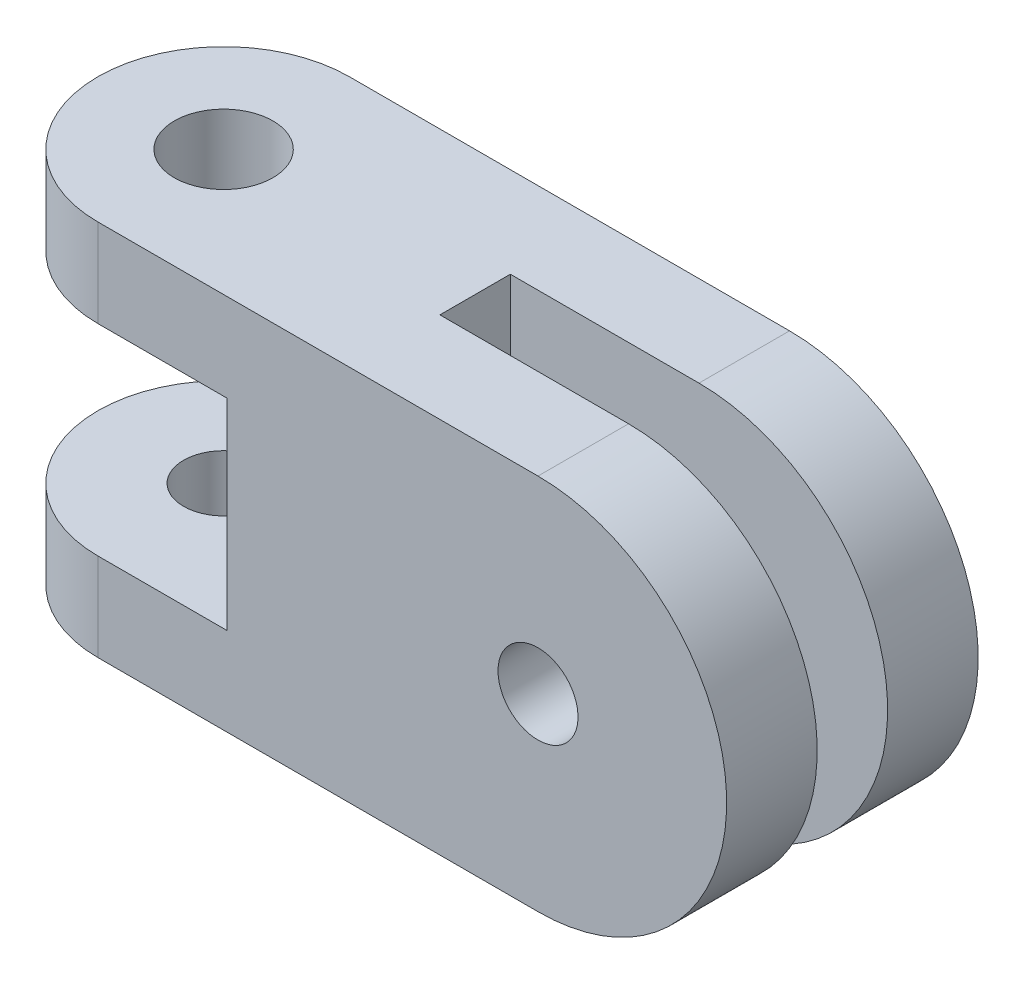
SolidWorks part; units mm, degrees
ref_plane "Front Plane" through (0, 0, 0) normal (0, 0, 1) x (1, 0, 0)
ref_plane "Top Plane" through (0, 0, 0) normal (0, 1, 0) x (1, 0, 0)
ref_plane "Right Plane" through (0, 0, 0) normal (1, 0, 0) x (0, 0, -1)
sketch "Sketch1" plane through (0, 0, 0) normal (0, 1, 0) x (1, 0, 0)
  line L0 (0, 0) -> (-15.875, 0) construction
  line L1 (0, -6.35) -> (-15.875, -6.35)
  line L2 (0, 6.35) -> (-15.875, 6.35)
  line L3 (0, 6.35) -> (0, -6.35)
  arc A1 (-15.875, 6.35) -> (-15.875, -6.35) centre (-15.875, 0) ccw
  point P3 (-7.9375, 0)
  point P8 (-16.925, 6.2626)
  dimension "D2" = 6.35
  dimension "D1" = 15.875
extrude "Boss-Extrude1" add sketch "Sketch1" along normal mid plane 19.05
sketch "Sketch2" plane through (0, 0, 6.35) normal (0, 0, 1) x (1, 0, 0)
  line L0 (0, 0) -> (6.35, 0) construction
  line L1 (0, 9.525) -> (0, -9.525) construction
  line L2 (0, 9.525) -> (6.35, 9.525)
  line L3 (0, -9.525) -> (6.35, -9.525)
  line L4 (-15.875, 9.525) -> (0, 9.525) construction
  arc A0 (0, 9.525) -> (0, -9.525) centre (0, 0) ccw
  arc A1 (6.35, -9.525) -> (6.35, 9.525) centre (6.35, 0) ccw
  point P4 (3.175, 0)
  dimension "D1" = 6.35
extrude "Boss-Extrude2" add sketch "Sketch2" against normal up to surface (12.7 mm away) up to face at (-7.9375, 0, -6.35)
sketch "Sketch3" plane through (0, 0, 0) normal (0, 1, 0) x (1, 0, 0)
  line L0 (6.35, 6.35) -> (-15.875, 6.35) construction
  line L1 (-15.875, -6.35) -> (6.35, -6.35) construction
  line L2 (-9.3515, 6.35) -> (-15.875, 6.35)
  line L3 (-15.875, -6.35) -> (-9.3515, -6.35)
  line L4 (-9.3515, -6.35) -> (-9.3515, 6.35)
  arc A0 (-15.875, 6.35) -> (-15.875, -6.35) centre (-15.875, 0) ccw construction
  arc A1 (-15.875, 6.35) -> (-15.875, -6.35) centre (-15.875, 0) ccw
  dimension "D1" = 6.5235
extrude "Cut-Extrude1" cut sketch "Sketch3" against normal mid plane 10.16
hole_wizard "#10-32 Tapped Hole1" positions "Sketch4" profile "Sketch5" tap size "#10-32" standard "ANSI Inch"
sketch "Sketch4" plane through (0, -5.08, 0) normal (0, 1, 0) x (1, 0, 0)
  point P0 (-15.875, 0)
sketch "Sketch5" plane through (-15.875, -5.08, 0) normal (1, 0, 0) x (0, 0, 1)
  line L0 (0, 0) -> (0, 4.445)
  line L1 (0, 4.445) -> (2.0193, 4.445)
  line L2 (2.0193, 4.445) -> (2.0193, 0)
  line L5 (2.0193, 0) -> (0, 0)
  line L11 (0, -6.35) -> (0, 107.95) construction
  dimension "Thru Tap Drill Dia." = 4.0386
  dimension "Thru Tap Drill Depth" = 4.445
cosmetic thread "Hole Thread1" parameters "D2"=4.826
hole_wizard "#10 Clearance Hole1" positions "Sketch6" profile "Sketch8" hole size "#10" standard "ANSI Inch"
sketch "Sketch6" plane through (0, 9.525, 0) normal (0, 1, 0) x (1, 0, 0)
  point P0 (-15.875, 0)
sketch "Sketch8" plane through (-15.875, 9.525, 0) normal (1, 0, 0) x (0, 0, 1)
  line L0 (0, 0) -> (0, 16.0997)
  line L1 (0, 16.0997) -> (2.4892, 14.604)
  line L2 (2.4892, 14.604) -> (2.4892, 0)
  line L5 (2.4892, 0) -> (0, 0)
  line L10 (0, 16.0997) -> (-2.4892, 14.604) construction
  line L11 (0, -6.35) -> (0, 107.95) construction
  dimension "Hole Dia." = 4.9784
  dimension "Hole Depth" = 14.604
  dimension "Drill Angle" = 118
sketch "Sketch9" plane through (0, 0, 0) normal (0, 0, 1) x (1, 0, 0)
  line L0 (-3.175, 0) -> (-3.175, -9.525)
  line L1 (-3.175, -9.525) -> (6.35, -9.525)
  line L3 (6.35, 9.525) -> (-3.175, 9.525)
  line L4 (-3.175, 9.525) -> (-3.175, 0)
  line L5 (6.35, -9.525) -> (-15.875, -9.525) construction
  arc A0 (6.35, -9.525) -> (6.35, 9.525) centre (6.35, 0) ccw
  arc A1 (6.35, -9.525) -> (6.35, 9.525) centre (6.35, 0) ccw construction
  point P8 (-1.5875, -7.9375)
  point P14 (0, 0)
extrude "Cut-Extrude2" cut sketch "Sketch9" along normal mid plane 3.556
hole_wizard "#10 Clearance Hole2" positions "Sketch10" profile "Sketch11" hole size "#10" standard "ANSI Inch"
sketch "Sketch10" plane through (0, 0, -6.35) normal (0, 0, -1) x (-1, 0, 0)
  point P0 (-6.35, 0)
sketch "Sketch11" plane through (6.35, 0, -6.35) normal (1, 0, 0) x (0, 1, 0)
  line L0 (0, 0) -> (0, 9.6227)
  line L1 (0, 9.6227) -> (2.4892, 8.127)
  line L2 (2.4892, 8.127) -> (2.4892, 0)
  line L5 (2.4892, 0) -> (0, 0)
  line L10 (0, 9.6227) -> (-2.4892, 8.127) construction
  line L11 (0, -6.35) -> (0, 107.95) construction
  dimension "Hole Dia." = 4.9784
  dimension "Hole Depth" = 8.127
  dimension "Drill Angle" = 118
hole_wizard "#10-32 Tapped Hole2" positions "Sketch12" profile "Sketch13" tap size "#10-32" standard "ANSI Inch" end condition through all
sketch "Sketch12" plane through (0, 0, 1.778) normal (0, 0, -1) x (-1, 0, 0)
  point P0 (-6.35, 0)
sketch "Sketch13" plane through (6.35, 0, 1.778) normal (1, 0, 0) x (0, 1, 0)
  line L0 (0, 0) -> (0, 4.572)
  line L1 (0, 4.572) -> (2.0193, 4.572)
  line L2 (2.0193, 4.572) -> (2.0193, 0)
  line L5 (2.0193, 0) -> (0, 0)
  line L11 (0, -6.35) -> (0, 107.95) construction
  dimension "Thru Tap Drill Dia." = 4.0386
  dimension "Thru Tap Drill Depth" = 4.572
cosmetic thread "Hole Thread2" parameters "D2"=4.826
equation "\"D1@Sketch3\"=.1875+1.38mm+.015"
